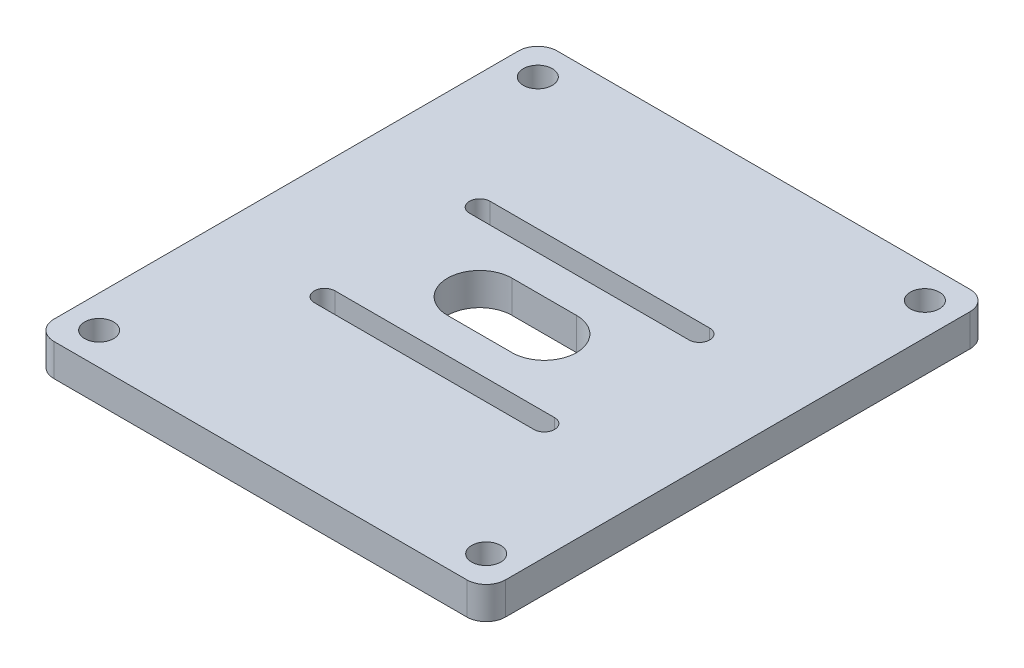
SolidWorks part; units mm, degrees
ref_plane "Front Plane" through (0, 0, 0) normal (0, 0, 1) x (1, 0, 0)
ref_plane "Top Plane" through (0, 0, 0) normal (0, 1, 0) x (1, 0, 0)
ref_plane "Right Plane" through (0, 0, 0) normal (1, 0, 0) x (0, 0, -1)
sketch "Sketch1" plane through (0, 0, 0) normal (0, 1, 0) x (1, 0, 0)
  line L0 (-22.0208, 12.0208) -> (12.0208, 12.0208) construction
  line L1 (-15, 15) -> (15, 15) construction
  line L2 (-15, 15) -> (-15, -15) construction
  line L3 (-15, -15) -> (15, -15) construction
  line L4 (15, 15) -> (15, -15) construction
  line L5 (-15, 15) -> (15, -15) construction
  line L6 (-15, -15) -> (15, 15) construction
  line L7 (-22.0208, 13.6208) -> (12.0208, 13.6208)
  line L8 (-22.0208, 10.4208) -> (12.0208, 10.4208)
  line L9 (0, 0) -> (-15, 0) construction
  line L10 (-22.0208, -12.0208) -> (12.0208, -12.0208) construction
  line L11 (-22.0208, -13.6208) -> (12.0208, -13.6208)
  line L12 (-22.0208, -10.4208) -> (12.0208, -10.4208)
  line L13 (-10, 0) -> (0, 0) construction
  line L14 (-10, 5) -> (0, 5)
  line L15 (-10, -5) -> (0, -5)
  line L16 (-5, 0) -> (-5, 39) construction
  line L18 (-40, 39) -> (-40, -39)
  line L20 (30, 39) -> (30, -39)
  line L21 (-36.0227, 39) -> (26.0227, -39) construction
  line L22 (-36.0227, -39) -> (26.0227, 39) construction
  line L25 (-40, -39) -> (30, -39)
  line L29 (-40, 39) -> (30, 39)
  line L32 (-15, 0) -> (-40, 0) construction
  circle A0 centre (0, 0) radius 17 construction
  circle A1 centre (-12.0208, 12.0208) radius 1.6 construction
  circle A2 centre (12.0208, 12.0208) radius 1.6 construction
  arc A3 (-22.0208, 13.6208) -> (-22.0208, 10.4208) centre (-22.0208, 12.0208) ccw
  arc A4 (12.0208, 10.4208) -> (12.0208, 13.6208) centre (12.0208, 12.0208) ccw
  arc A6 (-22.0208, -13.6208) -> (-22.0208, -10.4208) centre (-22.0208, -12.0208) cw
  arc A7 (12.0208, -10.4208) -> (12.0208, -13.6208) centre (12.0208, -12.0208) cw
  arc A8 (-10, 5) -> (-10, -5) centre (-10, 0) ccw
  arc A9 (0, -5) -> (0, 5) centre (0, 0) ccw
  circle A10 centre (-35, 34) radius 2.25
  circle A11 centre (25, 34) radius 2.25
  circle A12 centre (25, -34) radius 2.25
  circle A13 centre (-35, -34) radius 2.25
  point P0 (0, 0)
  point P12 (-22.0208, 12.0208)
  point P14 (-5, 12.0208)
  point P19 (-5, 0)
  point P23 (-5, -12.0208)
  point P28 (-10, 0)
  point P30 (-5, 0)
  point P38 (-35, 34)
  dimension "D3" = 34
  dimension "D4" = 10
  dimension "D6" = 1.6
  dimension "D7" = 1.6
  dimension "D8" = 5
  dimension "D12" = 4.5
  dimension "D1" = 30
  dimension "D2" = 30
  dimension "D5" = 10
  dimension "D9" = 78
  dimension "D10" = 5
  dimension "D11" = 5
extrude "Boss-Extrude1" add sketch "Sketch1" along normal blind 5 contours L29 L18 L25 L20 A9 L15 A8 L14 A4 L8 A3 L7 L12 A7 L11 A6
fillet "Fillet1" radius 3 4 edges at (-40, 2.5, 39) (30, 2.5, 39) (30, 2.5, -39) (-40, 2.5, -39)
